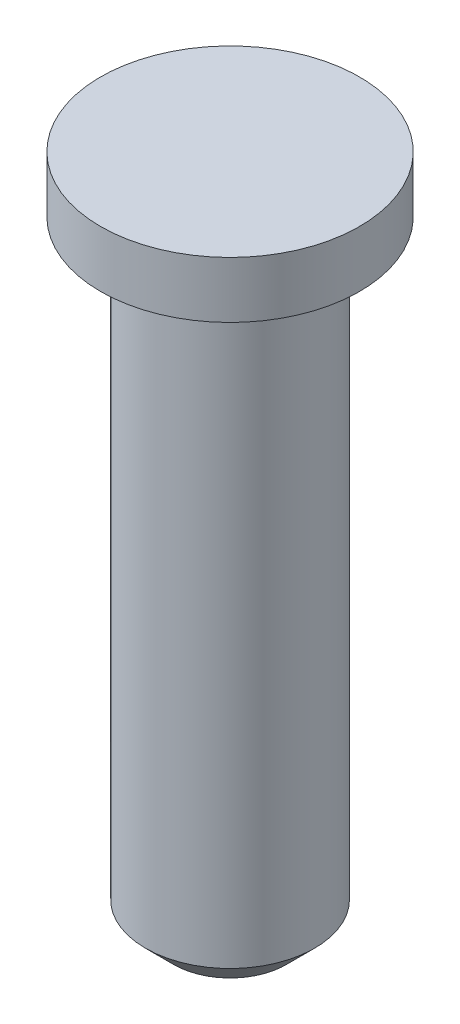
SolidWorks part; units mm, degrees
material "acero"
ref_plane "Alzado" through (0, 0, 0) normal (0, 0, 1) x (1, 0, 0)
ref_plane "Planta" through (0, 0, 0) normal (0, 1, 0) x (1, 0, 0)
ref_plane "Vista lateral" through (0, 0, 0) normal (1, 0, 0) x (0, 0, -1)
sketch "Croquis1" plane through (0, 0, 0) normal (0, 0, 1) x (1, 0, 0)
  line L0 (0, 0) -> (0, -60.9498) construction
  line L1 (0, 0) -> (2.3, 0)
  line L2 (2.3, 0) -> (2.3, -1)
  line L3 (2.3, -1) -> (1.5, -1)
  line L4 (1.5, -1) -> (1.5, -12)
  line L5 (1.5, -12) -> (0, -12)
  line L6 (0, -12) -> (0, 0)
  dimension "D1" = 12
  dimension "D2" = 1
  dimension "D3" = 4.6
  dimension "D4" = 3
revolve "Revolución1" add sketch "Croquis1" angle 360 about L0
chamfer "Chaflán1" distance 0.5 angle 45 1 edges at (0, -12, 1.5)
